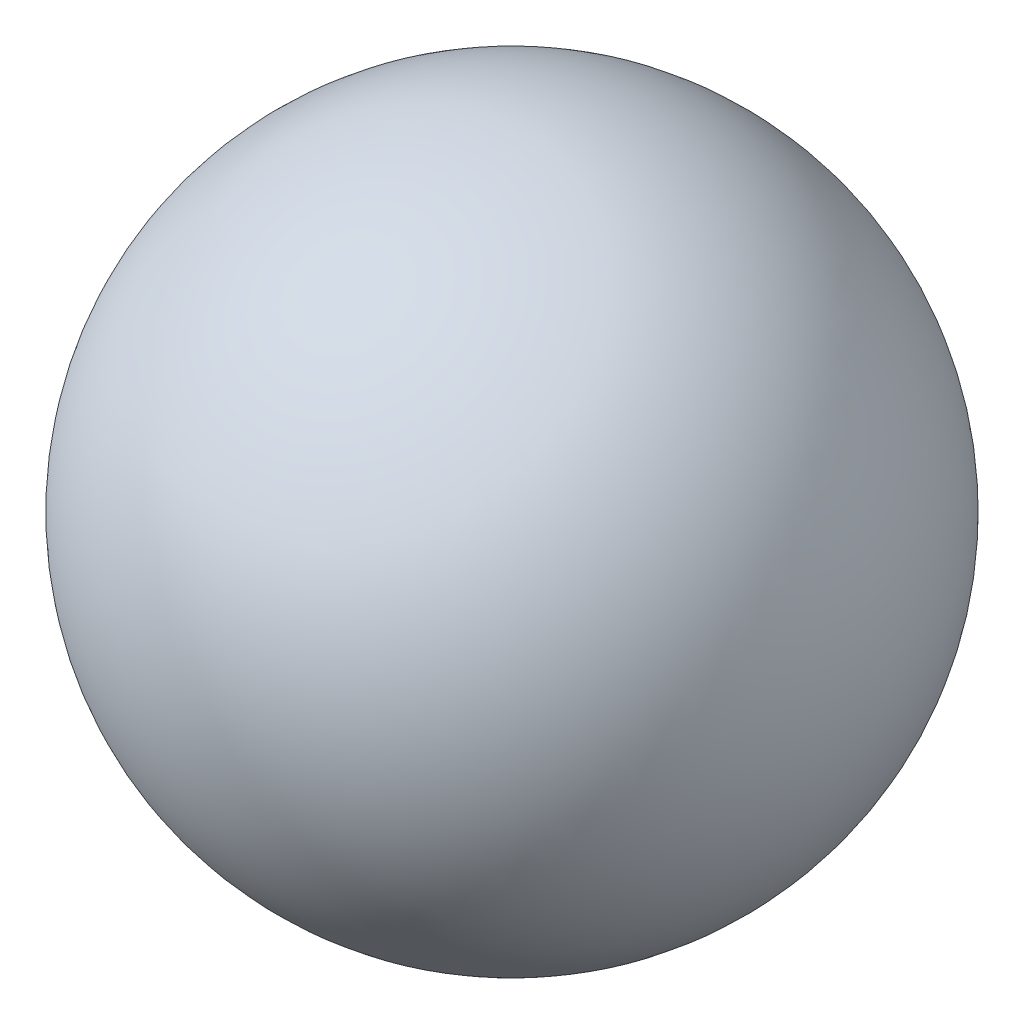
SolidWorks part; units mm, degrees
ref_plane "前视基准面" through (0, 0, 0) normal (0, 0, 1) x (1, 0, 0)
ref_plane "上视基准面" through (0, 0, 0) normal (0, 1, 0) x (1, 0, 0)
ref_plane "右视基准面" through (0, 0, 0) normal (1, 0, 0) x (0, 0, -1)
sketch "草图1" plane through (0, 0, 0) normal (0, 0, 1) x (1, 0, 0)
  line L0 (0, 0) -> (0, 59.5208) construction
  line L1 (0, -20) -> (0, 20)
  arc A1 (0, 20) -> (0, -20) centre (0, 0) ccw
  dimension "D1" = 40
revolve "旋转1" add sketch "草图1" angle 360 about L0
